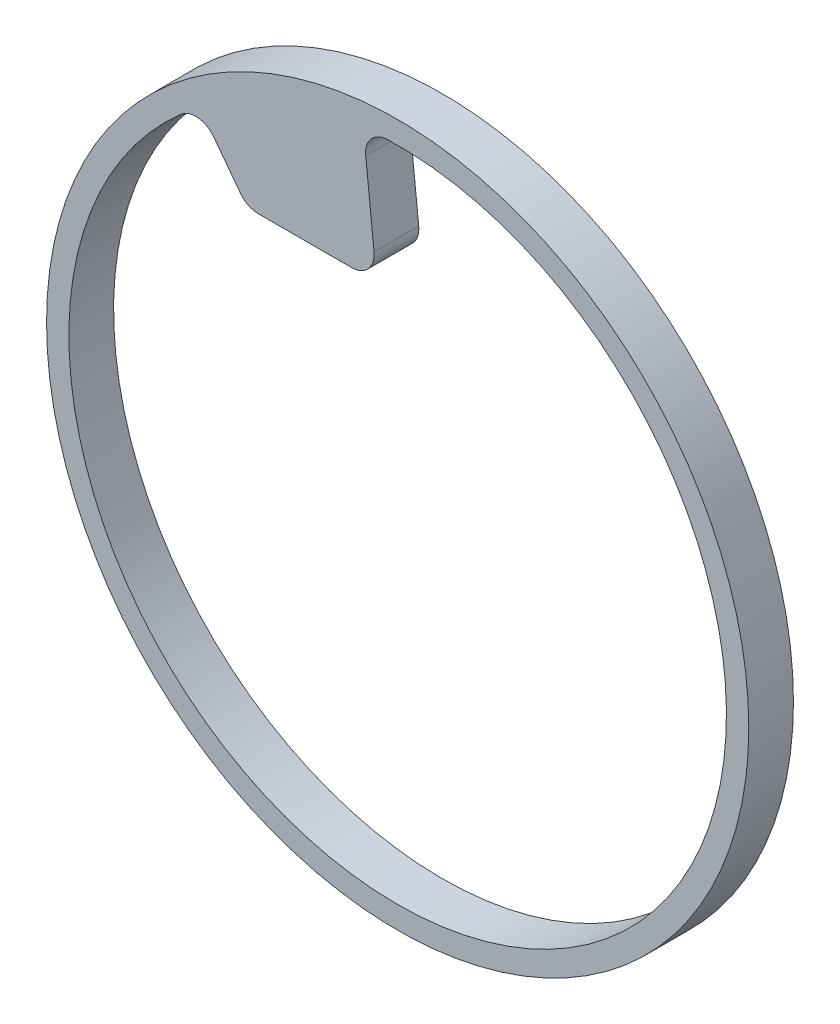
SolidWorks part; units mm, degrees
material "Acrylic (Medium-high impact)"
ref_plane "Front Plane" through (0, 0, 0) normal (0, 0, 1) x (1, 0, 0)
ref_plane "Top Plane" through (0, 0, 0) normal (0, 1, 0) x (1, 0, 0)
ref_plane "Right Plane" through (0, 0, 0) normal (1, 0, 0) x (0, 0, -1)
sketch "Sketch1" plane through (0, 0, 0) normal (0, 0, 1) x (1, 0, 0)
  circle A0 centre (0, 0) radius 24.9555
  circle A1 centre (0, 0) radius 24.9555 construction
  circle A2 centre (0, 0) radius 23.368
  dimension "D1" = 1.5875
extrude "Boss-Extrude1" add sketch "Sketch1" along normal blind 3.175
sketch "Sketch2" plane through (0, 0, 3.175) normal (0, 0, 1) x (1, 0, 0)
  line L0 (0, 0) -> (0, 23.368) construction
  line L1 (0, 0) -> (-2.4426, 23.24) construction
  line L2 (0, 0) -> (-14.0632, 18.6625) construction
  line L3 (-14.0632, 18.6625) -> (-10.7003, 14.1997)
  line L4 (-2.4426, 23.24) -> (-1.4925, 14.1997)
  line L5 (-10.7003, 14.1997) -> (-1.4925, 14.1997)
  circle A0 centre (0, 0) radius 23.368 construction
  circle A1 centre (0, 0) radius 17.78 construction
  arc A2 (-14.0632, 18.6625) -> (-2.4426, 23.24) centre (0, 0) cw
  dimension "D3" = 5.588
  dimension "D1" = 6
  dimension "D2" = 31
extrude "Boss-Extrude2" add sketch "Sketch2" against normal through all
fillet "Fillet1" radius 1.6002 4 edges at (-1.4925, 14.1997, 1.5875) (-10.7003, 14.1997, 1.5875) (-14.0632, 18.6625, 1.5875) (-2.4426, 23.24, 1.5875)
